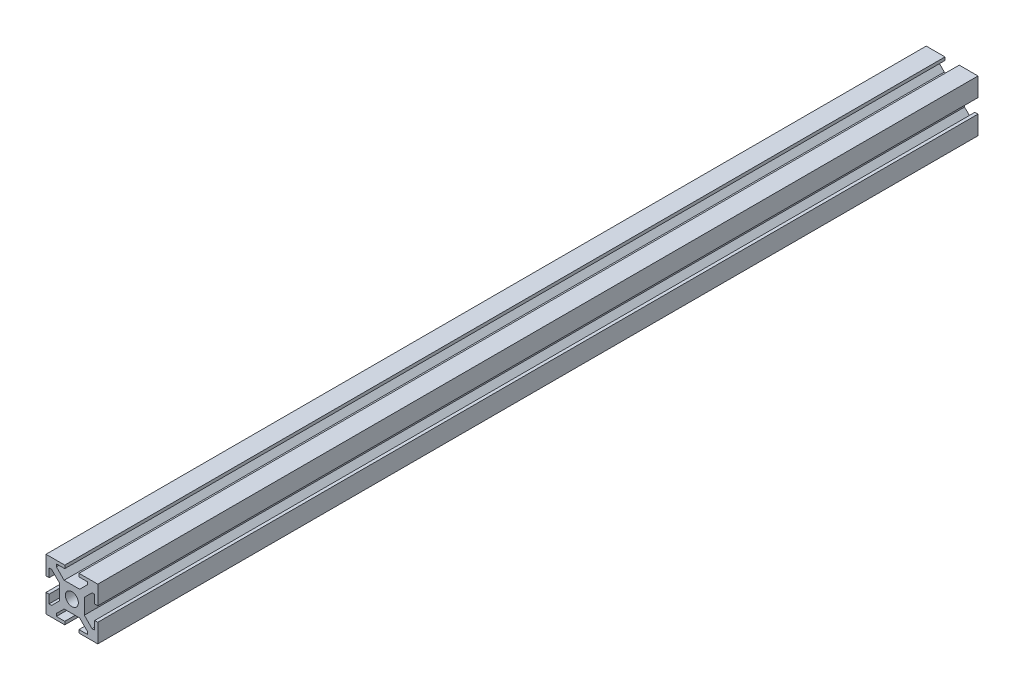
SolidWorks part; units mm, degrees
ref_plane "Plan de face" through (0, 0, 0) normal (0, 0, 1) x (1, 0, 0)
ref_plane "Plan de dessus" through (0, 0, 0) normal (0, 1, 0) x (1, 0, 0)
ref_plane "Plan de droite" through (0, 0, 0) normal (1, 0, 0) x (0, 0, -1)
sketch "Esquisse1" plane through (0, 0, 0) normal (0, 0, 1) x (1, 0, 0)
  line L1 (-22.5051, 0.0904) -> (-2.5051, 0.0904)
  line L2 (-22.5051, 0.0904) -> (-22.5051, -19.9096)
  line L3 (-22.5051, -19.9096) -> (-2.5051, -19.9096)
  line L4 (-2.5051, 0.0904) -> (-2.5051, -19.9096)
  dimension "D1" = 20
  dimension "D2" = 20
extrude "Boss.-Extru.1" add sketch "Esquisse1" along normal blind 340
sketch "Esquisse2" plane through (0, 0, 340) normal (0, 0, 1) x (1, 0, 0)
  line L0 (-22.5051, 0.0904) -> (-22.5051, -19.9096) construction
  line L1 (-22.5051, -7.1596) -> (-21.3051, -7.1596)
  line L2 (-22.5051, -7.1596) -> (-22.5051, -12.6596)
  line L3 (-22.5051, -12.6596) -> (-21.3051, -12.6596)
  line L4 (-21.3051, -7.1596) -> (-21.3051, -12.6596)
  line L5 (-2.5051, 0.0904) -> (-22.5051, 0.0904) construction
  line L6 (-15.2551, 0.0904) -> (-9.7551, 0.0904)
  line L7 (-15.2551, 0.0904) -> (-15.2551, -1.1096)
  line L8 (-15.2551, -1.1096) -> (-9.7551, -1.1096)
  line L9 (-9.7551, 0.0904) -> (-9.7551, -1.1096)
  line L10 (-2.5051, -19.9096) -> (-2.5051, 0.0904) construction
  line L11 (-2.5051, -7.1596) -> (-3.7051, -7.1596)
  line L12 (-2.5051, -7.1596) -> (-2.5051, -12.6596)
  line L13 (-2.5051, -12.6596) -> (-3.7051, -12.6596)
  line L14 (-3.7051, -7.1596) -> (-3.7051, -12.6596)
  line L15 (-22.5051, -19.9096) -> (-2.5051, -19.9096) construction
  line L16 (-15.2551, -19.9096) -> (-9.7551, -19.9096)
  line L17 (-15.2551, -19.9096) -> (-15.2551, -18.7096)
  line L18 (-15.2551, -18.7096) -> (-9.7551, -18.7096)
  line L19 (-9.7551, -19.9096) -> (-9.7551, -18.7096)
  dimension "D1" = 1.2
  dimension "D2" = 1.2
  dimension "D3" = 1.2
  dimension "D4" = 1.2
  dimension "D5" = 5.5
  dimension "D6" = 5.5
  dimension "D7" = 5.5
  dimension "D8" = 5.5
  dimension "D9" = 7.25
  dimension "D10" = 7.25
  dimension "D11" = 7.25
  dimension "D12" = 7.25
extrude "Enlèv. mat.-Extru.1" cut sketch "Esquisse2" against normal through all
sketch "Esquisse3" plane through (0, 0, 340) normal (0, 0, 1) x (1, 0, 0)
  line L0 (-15.2551, 0.0904) -> (-22.5051, 0.0904) construction
  line L1 (-21.3051, -15.9096) -> (-20.3051, -15.9096)
  line L2 (-21.3051, -15.9096) -> (-21.3051, -3.9096)
  line L3 (-21.3051, -3.9096) -> (-20.3051, -3.9096)
  line L4 (-17.3051, -12.9096) -> (-17.3051, -6.9096)
  line L5 (-18.5051, -1.1096) -> (-6.5051, -1.1096)
  line L6 (-18.5051, -1.1096) -> (-18.5051, -2.1096)
  line L7 (-15.5051, -5.1096) -> (-9.5051, -5.1096)
  line L8 (-6.5051, -1.1096) -> (-6.5051, -2.1096)
  line L9 (-3.7051, -3.9096) -> (-4.7051, -3.9096)
  line L10 (-3.7051, -3.9096) -> (-3.7051, -15.9096)
  line L11 (-3.7051, -15.9096) -> (-4.7051, -15.9096)
  line L12 (-7.7051, -6.9096) -> (-7.7051, -12.9096)
  line L13 (-6.5051, -18.7096) -> (-18.5051, -18.7096)
  line L14 (-6.5051, -18.7096) -> (-6.5051, -17.7096)
  line L15 (-9.5051, -14.7096) -> (-15.5051, -14.7096)
  line L16 (-18.5051, -18.7096) -> (-18.5051, -17.7096)
  line L17 (-2.5051, -7.1596) -> (-2.5051, 0.0904) construction
  line L18 (-15.2551, -1.1096) -> (-9.7551, -1.1096) construction
  line L19 (-3.7051, -7.1596) -> (-3.7051, -12.6596) construction
  line L20 (-9.7551, -19.9096) -> (-2.5051, -19.9096) construction
  line L21 (-22.5051, -12.6596) -> (-22.5051, -19.9096) construction
  line L22 (-22.5051, -19.9096) -> (-15.2551, -19.9096) construction
  line L23 (-15.5051, -14.7096) -> (-18.5051, -17.7096)
  line L24 (-20.3051, -15.9096) -> (-17.3051, -12.9096)
  line L25 (-6.5051, -17.7096) -> (-9.5051, -14.7096)
  line L26 (-4.7051, -15.9096) -> (-7.7051, -12.9096)
  line L27 (-4.7051, -3.9096) -> (-7.7051, -6.9096)
  line L28 (-9.5051, -5.1096) -> (-6.5051, -2.1096)
  line L29 (-18.5051, -2.1096) -> (-15.5051, -5.1096)
  line L30 (-20.3051, -3.9096) -> (-17.3051, -6.9096)
  point P1 (-17.3051, -3.9096)
  point P3 (-17.3051, -15.9096)
  point P5 (-6.5051, -5.1096)
  point P6 (-18.5051, -5.1096)
  point P9 (-7.7051, -15.9096)
  point P11 (-7.7051, -3.9096)
  point P13 (-18.5051, -14.7096)
  point P14 (-6.5051, -14.7096)
  point P24 (-6.1301, -19.9096)
  dimension "D1" = 4
  dimension "D2" = 4
  dimension "D3" = 4
  dimension "D4" = 4
  dimension "D5" = 12
  dimension "D6" = 4
  dimension "D7" = 12
  dimension "D8" = 4
  dimension "D9" = 0
  dimension "D10" = 0
  dimension "D11" = 4
  dimension "D12" = 12
  dimension "D13" = 12
  dimension "D14" = 4
  dimension "D15" = 1.2
  dimension "D16" = 1.2
  dimension "D17" = 3
  dimension "D18" = 3
  dimension "D19" = 3
  dimension "D20" = 3
  dimension "D21" = 3
  dimension "D22" = 3
  dimension "D23" = 3
  dimension "D24" = 3
  dimension "D25" = 3
  dimension "D26" = 3
  dimension "D27" = 3
  dimension "D28" = 3
  dimension "D29" = 3
  dimension "D30" = 3
  dimension "D31" = 3
  dimension "D32" = 3
extrude "Enlèv. mat.-Extru.2" cut sketch "Esquisse3" against normal through all
sketch "Esquisse4" plane through (0, 0, 340) normal (0, 0, 1) x (1, 0, 0)
  line L0 (-15.5051, -5.1096) -> (-9.5051, -5.1096) construction
  line L2 (-17.3051, -12.9096) -> (-17.3051, -6.9096) construction
  circle A0 centre (-12.5051, -9.9096) radius 2.5
  dimension "D1" = 5
  dimension "D2" = 4.8
  dimension "D3" = 4.8
extrude "Enlèv. mat.-Extru.3" cut sketch "Esquisse4" against normal through all
